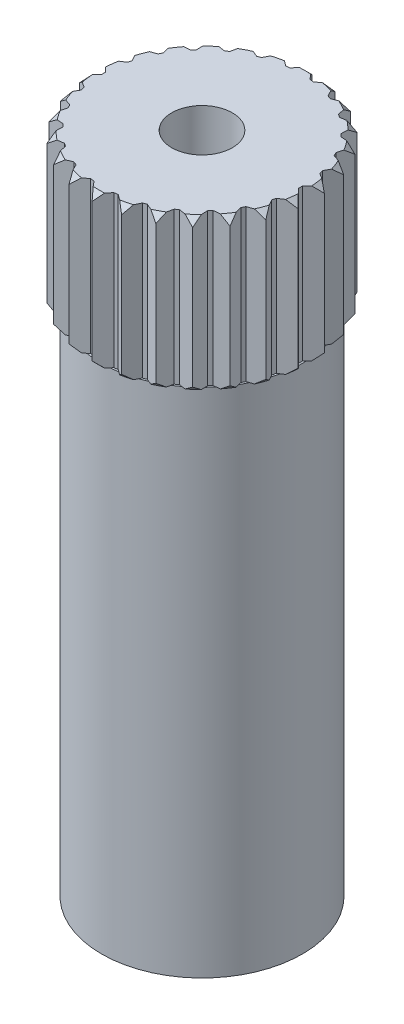
SolidWorks part; units mm, degrees
material "Brass"
ref_plane "Front Plane" through (0, 0, 0) normal (0, 0, 1) x (1, 0, 0)
ref_plane "Top Plane" through (0, 0, 0) normal (0, 1, 0) x (1, 0, 0)
ref_plane "Right Plane" through (0, 0, 0) normal (1, 0, 0) x (0, 0, -1)
sketch "Sketch12" plane through (0, 0, 0) normal (0, 1, 0) x (1, 0, 0)
  circle A0 centre (0, 0) radius 2.9
  dimension "D1" = 5.8
extrude "Boss-Extrude4" add sketch "Sketch12" along normal blind 13.5 separate body
sketch "Sketch13" plane through (0, 13.5, 0) normal (0, 1, 0) x (1, 0, 0)
  circle A2 centre (0, 0) radius 2.6
  circle A3 centre (0, 0) radius 2.9 construction
  dimension "D1" = 0.3
extrude "Boss-Extrude5" add sketch "Sketch13" along normal blind 4
sketch "Sketch14" plane through (0, 17.5, 0) normal (0, 1, 0) x (1, 0, 0)
  line L0 (0, 2.6) -> (0, 2.9) construction
  line L1 (0, 2.9) -> (-0.2629, 2.5867)
  line L2 (0, 2.9) -> (0.2629, 2.5867)
  line L3 (-0.2629, 2.5867) -> (0.2629, 2.5867) construction
  circle A0 centre (0, 0) radius 2.9 construction
  circle A1 centre (0, 0) radius 2.6
  arc A2 (0.2629, 2.5867) -> (-0.2629, 2.5867) centre (0, 0) ccw
  dimension "D2" = 80
  dimension "D3" = 0.5258
  dimension "D4" = 0.3
  dimension "D1" = 0
extrude "Boss-Extrude6" add sketch "Sketch14" against normal up to body (17.5 mm away) separate body
pattern_circular "CirPattern1" count 26 over 360 about axis through (0, 0, 0) along (0, 1, 0) of "Boss-Extrude6"
sketch "Sketch15" plane through (0, 0, 0) normal (1, 0, 0) x (0, 0, -1)
  line L0 (2.9, 17.3232) -> (2.9, 17.5)
  line L1 (2.9, 13.5) -> (2.9, 17.5) construction
  line L2 (2.9, 17.5) -> (2.7232, 17.5)
  line L3 (2.1682, 17.5) -> (2.5678, 17.5) construction
  line L4 (2.7232, 17.5) -> (2.9, 17.3232)
  dimension "D1" = 45
  dimension "D2" = 0.25
revolve "Cut-Revolve1" cut sketch "Sketch15" angle 360 about axis through (0, 17.5, 0) along (0, -1, 0)
sketch "Sketch16" plane through (0, 17.5, 0) normal (0, 1, 0) x (1, 0, 0)
  circle A0 centre (0, 0) radius 0.8
  dimension "D1" = 1.6
extrude "Cut-Extrude1" cut sketch "Sketch16" against normal blind 4
ref_plane "Plane1" through (-0.3638, 13.5, -2.5744) normal (-0.9902, 0, 0.1399) x (0.1399, 0, 0.9902)
sketch "Sketch17" plane through (0, 0, 0) normal (0, 0, 1) x (1, 0, 0)
  line L0 (2.9, 0) -> (2.65, 0)
  line L1 (-2.9, 0) -> (2.9, 0) construction
  line L2 (2.65, 0) -> (2.65, 13.5)
  line L3 (2.65, 13.5) -> (2.9, 13.5)
  line L4 (2.9, 13.5) -> (2.9, 0)
  line L5 (0, 0) -> (2.65, 0) construction
  line L6 (2.7115, 13.5) -> (2.3254, 13.5) construction
  dimension "D1" = 0.25
  dimension "D2" = 2.65
  dimension "D3" = 2.9
revolve "Cut-Revolve2" cut sketch "Sketch17" angle 360 about axis through (0, 13.5, 0) along (0, -1, 0)
ref_plane "Plane2" through (0, 15.5, 0) normal (0, 1, 0) x (1, 0, 0)
mirror "Mirror1" about plane through (0, 15.5, 0) normal (0, 1, 0) of "Cut-Revolve1"
